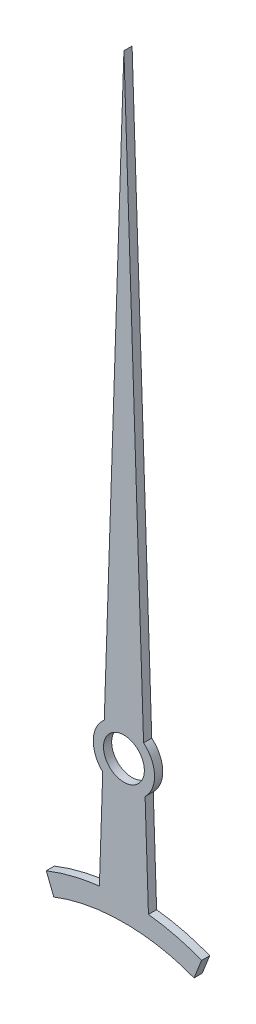
SolidWorks part; units mm, degrees
ref_plane "Alzado" through (0, 0, 0) normal (0, 0, 1) x (1, 0, 0)
ref_plane "Planta" through (0, 0, 0) normal (0, 1, 0) x (1, 0, 0)
ref_plane "Vista lateral" through (0, 0, 0) normal (1, 0, 0) x (0, 0, -1)
sketch "Croquis1" plane through (0, 0, 0) normal (0, 0, 1) x (1, 0, 0)
  line L0 (0, 0) -> (0, 15) construction
  line L1 (0, 0) -> (0, -3) construction
  line L2 (-0.5, 0) -> (-0.4989, 0.0333)
  line L3 (0, 15) -> (0.4808, 0.5756)
  line L4 (0.5181, -0.5423) -> (0.6, -3)
  line L5 (-0.5181, -0.5423) -> (-0.6, -3)
  line L6 (-1.9, -3.325) -> (-1.7156, -3.7897)
  line L7 (1.7156, -3.7897) -> (1.9, -3.325)
  line L8 (0.4989, 0.0333) -> (0.5, 0)
  line L9 (-0.4808, 0.5756) -> (0, 15)
  circle A0 centre (0, 0) radius 0.5
  circle A1 centre (0, 0) radius 0.75
  spline S0 degree 3 poles (-1.9, -3.325) (-1.4829, -3.1595) (-0.6523, -2.9542) (0.6523, -2.9542) (1.4829, -3.1595) (1.9, -3.325) knots 0 0 0 0 0.345361 0.654639 1 1 1 1
  spline S1 degree 1 poles (-1.7156, -3.7897) (1.7156, -3.7897) knots 0 0 1 1 construction
  spline S2 degree 3 poles (-1.7156, -3.7897) (-0.6525, -3.368) (0.6525, -3.368) (1.7156, -3.7897) knots 0 0 0 0 1 1 1 1
  dimension "D3" = 1
  dimension "D4" = 1.5
  dimension "D1" = 15
  dimension "D2" = 3
  dimension "D5" = 1.3
  dimension "D6" = 1.3
  dimension "D7" = 0.5
extrude "Saliente-Extruir1" add sketch "Croquis1" along normal blind 0.2
